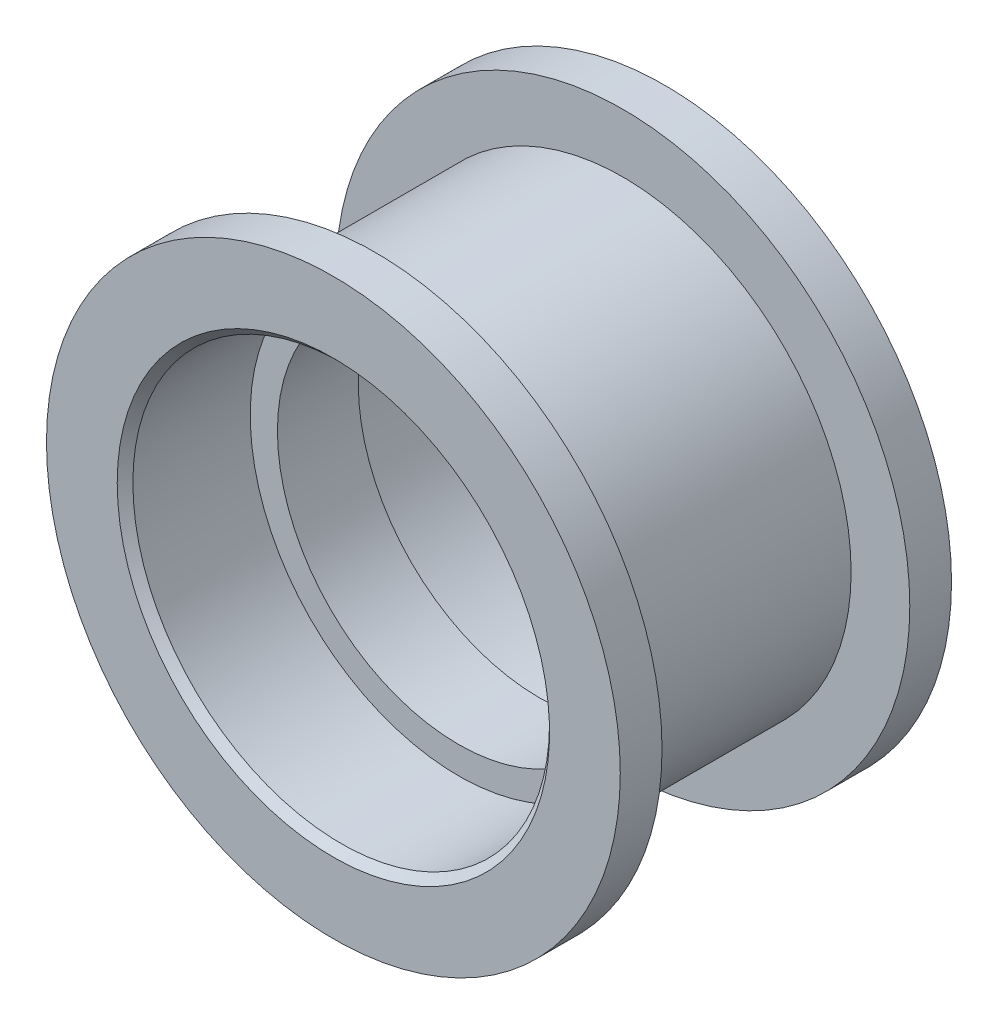
SolidWorks part; units mm, degrees
ref_plane "Front Plane" through (0, 0, 0) normal (0, 0, 1) x (1, 0, 0)
ref_plane "Top Plane" through (0, 0, 0) normal (0, 1, 0) x (1, 0, 0)
ref_plane "Right Plane" through (0, 0, 0) normal (1, 0, 0) x (0, 0, -1)
sketch "Sketch1" plane through (0, 0, 0) normal (1, 0, 0) x (0, 0, -1)
  line L0 (0, 0) -> (15, 0) construction
  line L1 (0, 0) -> (0, 11) construction
  line L2 (-1.55, 6.945) -> (1.55, 6.945) construction
  line L3 (-6.35, 7.9875) -> (6.35, 7.9875) construction
  line L4 (-6.35, 11) -> (6.35, 11) construction
  line L5 (-4.75, 8.75) -> (4.75, 8.75) construction
  line L6 (4.75, 8.75) -> (-4.75, 8.75)
  line L7 (-4.75, 8.75) -> (-4.75, 11)
  line L8 (-4.75, 11) -> (-6.35, 11)
  line L9 (-6.35, 11) -> (-6.35, 7.9875)
  line L10 (-6.35, 7.9875) -> (-1.55, 7.9875)
  line L11 (-1.55, 7.9875) -> (-1.55, 6.945)
  line L12 (-1.55, 6.945) -> (1.55, 6.945)
  line L13 (1.55, 7.9875) -> (1.55, 6.945)
  line L14 (6.35, 7.9875) -> (1.55, 7.9875)
  line L15 (6.35, 11) -> (6.35, 7.9875)
  line L16 (4.75, 11) -> (6.35, 11)
  line L17 (4.75, 8.75) -> (4.75, 11)
  point P10 (0, 11)
  point P11 (0, 7.9875)
  point P12 (0, 6.945)
  point P15 (0, 8.75)
  point P19 (0, 6.945)
  point P22 (0, 8.75)
  dimension "D1" = 15
  dimension "D2" = 11
  dimension "D3" = 12.7
  dimension "D4" = 12.7
  dimension "D5" = 3.1
  dimension "D6" = 6.945
  dimension "D7" = 7.9875
  dimension "D8" = 9.5
  dimension "D9" = 8.75
revolve "Revolve1" add sketch "Sketch1" angle 360 about L0
chamfer "Chamfer1" distance 0.3 angle 45 2 edges at (7.9875, 0, -6.35) (7.9875, 0, 6.35)
